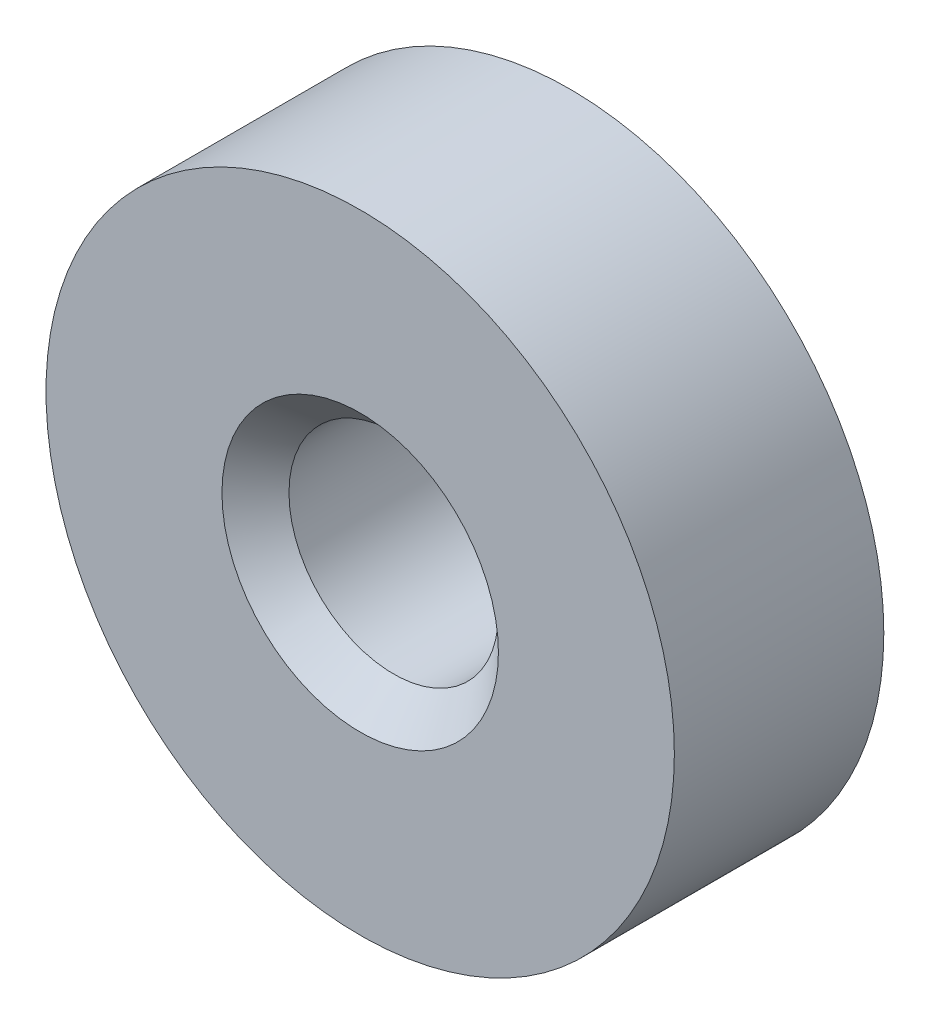
SolidWorks part; units mm, degrees
ref_plane "Front Plane" through (0, 0, 0) normal (0, 0, 1) x (1, 0, 0)
ref_plane "Top Plane" through (0, 0, 0) normal (0, 1, 0) x (1, 0, 0)
ref_plane "Right Plane" through (0, 0, 0) normal (1, 0, 0) x (0, 0, -1)
sketch "Sketch1" plane through (0, 0, 0) normal (0, 0, 1) x (1, 0, 0)
  circle A0 centre (0, 0) radius 4.7625
  circle A1 centre (0, 0) radius 14.2875
  dimension "D1" = 28.575
  dimension "D2" = 9.525
extrude "Boss-Extrude1" add sketch "Sketch1" along normal blind 9.525
chamfer "Chamfer1" distance 1.524 angle 45 2 edges at (4.7625, 0, 0) (4.7625, 0, 9.525)
